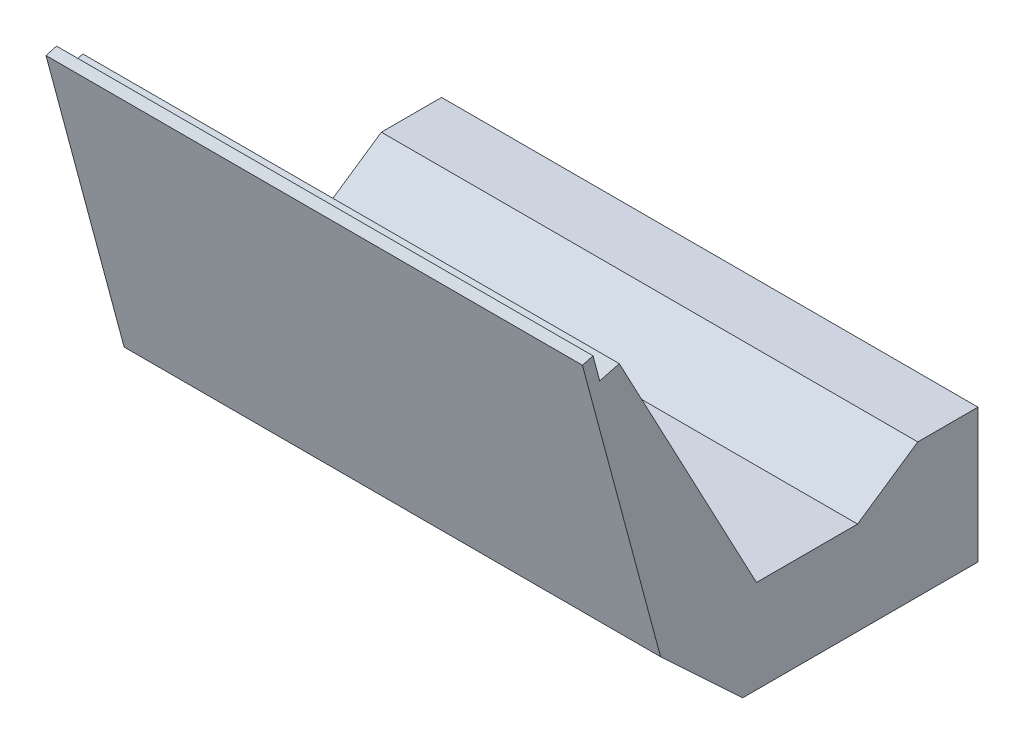
SolidWorks part; units mm, degrees
ref_plane "Front Plane" through (0, 0, 0) normal (0, 0, 1) x (1, 0, 0)
ref_plane "Top Plane" through (0, 0, 0) normal (0, 1, 0) x (1, 0, 0)
ref_plane "Right Plane" through (0, 0, 0) normal (1, 0, 0) x (0, 0, -1)
sketch "Sketch1" plane through (0, 0, 0) normal (1, 0, 0) x (0, 0, -1)
  line L0 (0, 0) -> (-50.7957, 0) construction
  line L1 (-62.3324, 50.7829) -> (-61.103, 46.1948)
  line L2 (-64.2642, 50.2653) -> (-49.9918, -3)
  line L3 (8, -17) -> (-35, -17)
  line L4 (-49.9918, -3) -> (-35, -17)
  line L5 (-64.2642, 50.2653) -> (-61.0658, 51.1223)
  line L6 (-61.103, 46.1948) -> (-57.5374, 47.1502)
  line L7 (-57.5374, 47.1502) -> (-32.4673, 0)
  line L8 (8, -17) -> (8, 7.5)
  line L9 (8, 7.5) -> (-3, 7.5)
  line L10 (-3, 7.5) -> (-14, 0)
  line L11 (-14, 0) -> (-32.4673, 0)
  dimension "D1" = 17
  dimension "D2" = 35
  dimension "D3" = 3
  dimension "D4" = 24.5
  dimension "D5" = 8
  dimension "D6" = 11
  dimension "D7" = 11
extrude "Boss-Extrude1" add sketch "Sketch1" along normal mid plane 98
